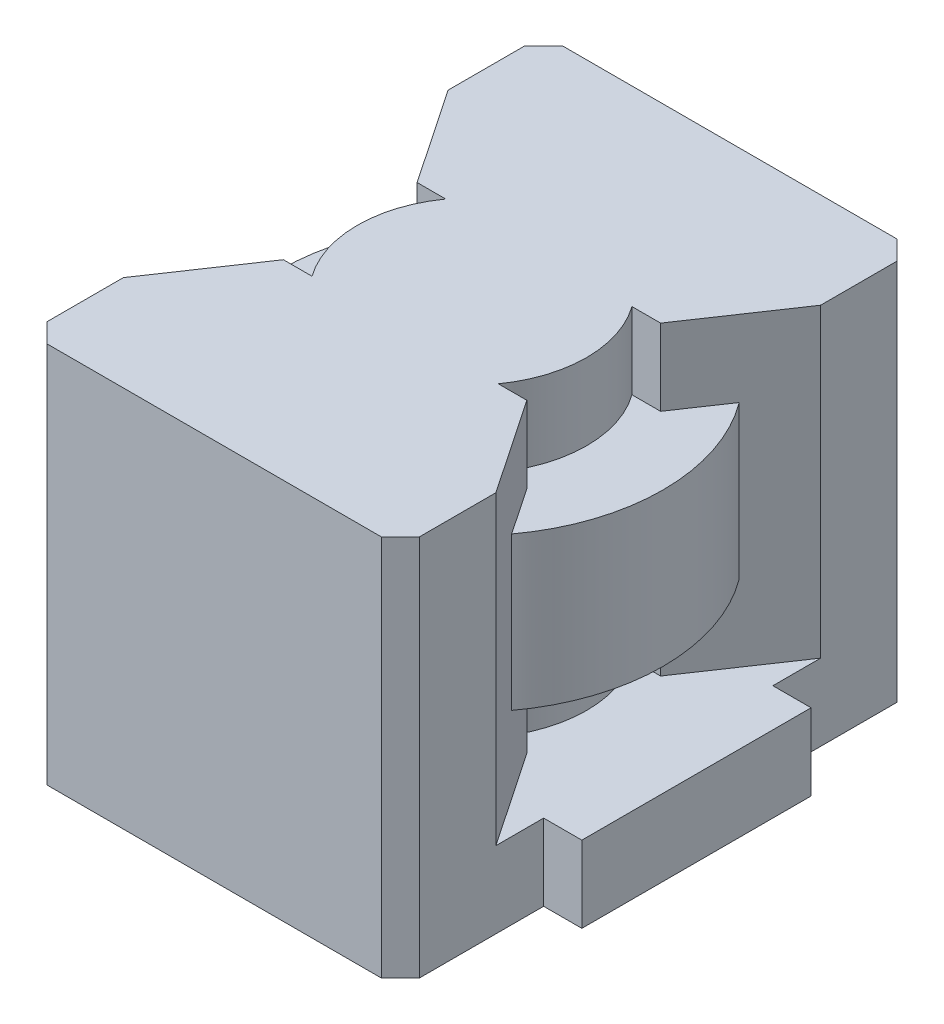
SolidWorks part; units mm, degrees
ref_plane "Front Plane" through (0, 0, 0) normal (0, 0, 1) x (1, 0, 0)
ref_plane "Top Plane" through (0, 0, 0) normal (0, 1, 0) x (1, 0, 0)
ref_plane "Right Plane" through (0, 0, 0) normal (1, 0, 0) x (0, 0, -1)
sketch "Sketch1" plane through (0, 0, 0) normal (0, 1, 0) x (1, 0, 0)
  line L1 (-9.75, -13.5) -> (9.75, -13.5)
  line L2 (-9.75, -13.5) -> (-9.75, 13.5)
  line L3 (-9.75, 13.5) -> (9.75, 13.5)
  line L4 (9.75, -13.5) -> (9.75, 13.5)
  line L5 (-9.75, -13.5) -> (9.75, 13.5) construction
  line L6 (-9.75, 13.5) -> (9.75, -13.5) construction
  line L7 (-9.75, 6) -> (-11.75, 6)
  line L8 (-9.75, 6) -> (-9.75, -6)
  line L9 (-9.75, -6) -> (-11.75, -6)
  line L10 (-11.75, 6) -> (-11.75, -6)
  line L11 (9.75, -6) -> (11.75, -6)
  line L12 (9.75, -6) -> (9.75, 6)
  line L13 (9.75, 6) -> (11.75, 6)
  line L14 (11.75, -6) -> (11.75, 6)
  point P0 (0, 0)
  point P14 (-11.75, 0)
  dimension "D1" = 19.5
  dimension "D2" = 27
  dimension "D3" = 2
  dimension "D4" = 12
extrude "Boss-Extrude1" add sketch "Sketch1" along normal blind 4 contours L7 L10 L9 L2 | L1 L4 L3 L2 | L11 L14 L13 L4
sketch "Sketch2" plane through (0, 4, 0) normal (0, 1, 0) x (1, 0, 0)
  line L0 (-9.75, 13.5) -> (9.75, -13.5) construction
  line L1 (-9.75, -8.5) -> (-6.3734, -3.5)
  line L2 (-9.75, 13.5) -> (9.75, 13.5)
  line L3 (-9.75, 13.5) -> (-9.75, 8.5)
  line L4 (-9.75, 8.5) -> (9.75, 8.5)
  line L5 (9.75, 13.5) -> (9.75, 8.5)
  line L6 (9.75, -13.5) -> (-9.75, -13.5)
  line L7 (9.75, -13.5) -> (9.75, -8.5)
  line L8 (9.75, -8.5) -> (-9.75, -8.5)
  line L9 (-9.75, -13.5) -> (-9.75, -8.5)
  line L10 (-6.3734, -3.5) -> (-4.8734, -3.5)
  line L11 (0, 0) -> (0, 50000) construction
  line L12 (-9.75, 6) -> (-11.75, 6)
  line L13 (-11.75, 6) -> (-11.75, -6)
  line L14 (-11.75, -6) -> (-9.75, -6)
  line L15 (-9.75, -6) -> (-9.75, -13.5)
  line L16 (-9.75, -13.5) -> (9.75, -13.5)
  line L17 (9.75, -13.5) -> (9.75, -6)
  line L18 (9.75, -6) -> (11.75, -6)
  line L19 (11.75, -6) -> (11.75, 6)
  line L20 (11.75, 6) -> (9.75, 6)
  line L21 (9.75, 6) -> (9.75, 13.5)
  line L22 (9.75, 13.5) -> (-9.75, 13.5)
  line L23 (-9.75, 13.5) -> (-9.75, 6)
  line L24 (-9.75, 6) -> (-11.75, 6) construction
  line L25 (-11.75, 6) -> (-11.75, -6) construction
  line L26 (-11.75, -6) -> (-9.75, -6) construction
  line L27 (-9.75, -6) -> (-9.75, -13.5) construction
  line L28 (-9.75, -13.5) -> (9.75, -13.5) construction
  line L29 (9.75, -13.5) -> (9.75, -6) construction
  line L30 (9.75, -6) -> (11.75, -6) construction
  line L31 (11.75, -6) -> (11.75, 6) construction
  line L32 (11.75, 6) -> (9.75, 6) construction
  line L33 (9.75, 6) -> (9.75, 13.5) construction
  line L34 (9.75, 13.5) -> (-9.75, 13.5) construction
  line L35 (-9.75, 13.5) -> (-9.75, 6) construction
  line L36 (1.4292, 0) -> (50001.4292, 0) construction
  line L37 (9.75, -8.5) -> (6.3734, -3.5)
  line L38 (6.3734, -3.5) -> (4.8734, -3.5)
  line L39 (9.75, 8.5) -> (6.3734, 3.5)
  line L40 (6.3734, 3.5) -> (4.8734, 3.5)
  line L41 (-9.75, 8.5) -> (-6.3734, 3.5)
  line L42 (-6.3734, 3.5) -> (-4.8734, 3.5)
  circle A0 centre (0, 0) radius 6
  point P14 (-5.6234, -3.5)
  line M32 (-9.75, -6) -> (-9.75, -13.5)
  line M33 (-9.75, -13.5) -> (9.75, -13.5)
  line M34 (9.75, -13.5) -> (9.75, -6)
  line M38 (9.75, 6) -> (9.75, 13.5)
  line M39 (9.75, 13.5) -> (-9.75, 13.5)
  line M40 (-9.75, 13.5) -> (-9.75, 6)
  dimension "D3" = 12
  dimension "D2" = 5
  dimension "D4" = 5
  dimension "D5" = 1.5
  dimension "D1" = 0
extrude "Boss-Extrude2" add sketch "Sketch2" along normal blind 16 contours A0 L40 L39 L4 L41 L42 | L4 M40 M38 M39 | A0 | A0 L10 L1 L8 L37 L38 | L8 M34 M32 M33
sketch "Sketch3" plane through (0, 4, 0) normal (0, 1, 0) x (1, 0, 0)
  circle A0 centre (0, 0) radius 10
  dimension "D1" = 20
extrude "Boss-Extrude3" add sketch "Sketch3" along normal blind 8 from offset 4
chamfer "Chamfer1" distance 1 angle 45 4 edges at (9.75, 10, -13.5) (9.75, 10, 13.5) (-9.75, 10, 13.5) (-9.75, 10, -13.5)
